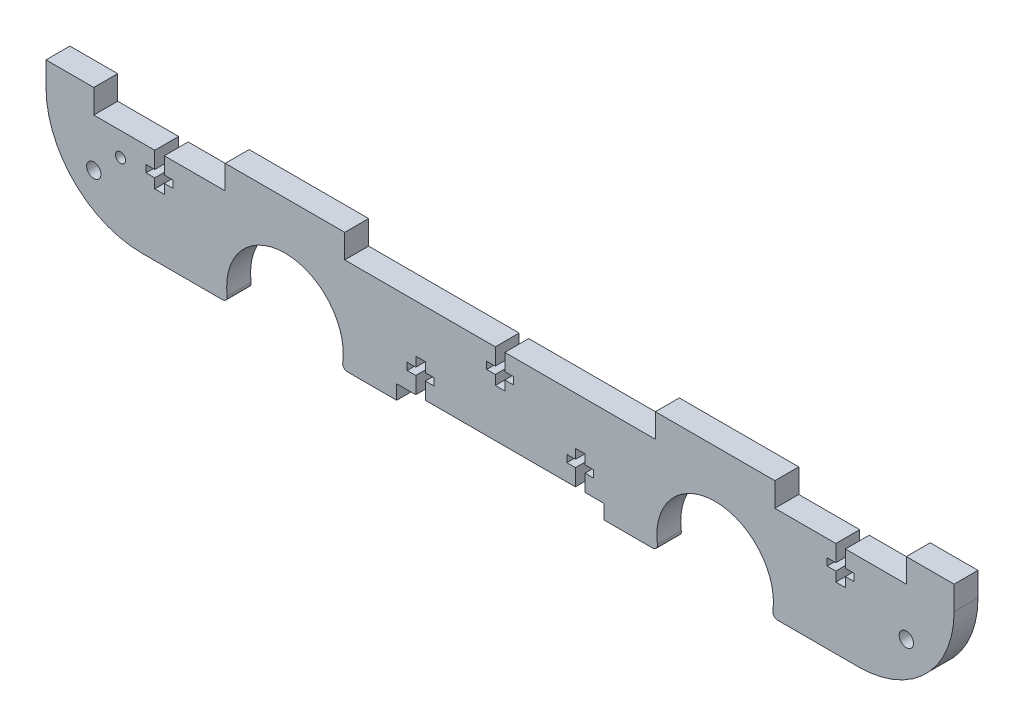
SolidWorks part; units mm, degrees
material "Acrílico (médio-alto impacto)"
ref_plane "Plano frontal" through (0, 0, 0) normal (0, 0, 1) x (1, 0, 0)
ref_plane "Plano superior" through (0, 0, 0) normal (0, 1, 0) x (1, 0, 0)
ref_plane "Plano direito" through (0, 0, 0) normal (1, 0, 0) x (0, 0, -1)
sketch "Esboço1" plane through (0, 0, 0) normal (0, 0, 1) x (1, 0, 0)
  line L1 (20, 0) -> (170, 0)
  line L2 (0, 20) -> (0, 25)
  line L3 (0, 25) -> (190, 25)
  line L4 (190, 20) -> (190, 25)
  arc A0 (0, 20) -> (20, 0) centre (20, 20) ccw
  arc A1 (190, 20) -> (170, 0) centre (170, 20) cw
  point P7 (0, 0)
  point P10 (190, 0)
  dimension "D3" = 20
  dimension "D1" = 190
  dimension "D2" = 25
extrude "Ressalto-extrusão1" add sketch "Esboço1" along normal blind 5
sketch "Esboço2" plane through (0, 0, 0) normal (0, 0, -1) x (-1, 0, 0)
  line L0 (0, 0) -> (-190, 0) construction
  line L1 (0, 25) -> (0, 0) construction
  line L2 (-190, 25) -> (-190, 0) construction
  line L3 (0, 2.8) -> (-190, 2.8) construction
  line L4 (-95, 25) -> (-95, 0) construction
  line L5 (-190, 25) -> (0, 25) construction
  circle A0 centre (-50, 2.8) radius 12.2
  circle A1 centre (-140, 2.8) radius 12.2
  dimension "D1" = 24.4
  dimension "D2" = 50
extrude "Corte-extrusão1" cut sketch "Esboço2" against normal through all
fillet "Filete1" radius 1 4 edges at (38.1257, 0, 2.5) (61.8743, 0, 2.5) (128.1257, 0, 2.5) (151.8743, 0, 2.5)
sketch "Esboço3" plane through (0, 0, 0) normal (0, 0, -1) x (-1, 0, 0)
  line L0 (-152.5, 2.8) -> (-152.5, 25) construction
  line L1 (-190, 25) -> (0, 25) construction
  line L2 (-127.5, 2.8) -> (-127.5, 25) construction
  line L3 (-62.5, 2.8) -> (-62.5, 25) construction
  line L4 (-37.5, 2.8) -> (-37.5, 25) construction
  line L5 (-10, 25) -> (-10, 0) construction
  line L6 (-180, 25) -> (-180, 0) construction
  line L7 (-190, 20) -> (0, 20) construction
  line L8 (-50, 15) -> (-50, 25) construction
  line L9 (-180, 25) -> (-152.5, 25)
  line L10 (-180, 25) -> (-180, 20)
  line L11 (-180, 20) -> (-152.5, 20)
  line L12 (-152.5, 25) -> (-152.5, 20)
  line L13 (-127.5, 25) -> (-62.5, 25)
  line L14 (-127.5, 25) -> (-127.5, 20)
  line L15 (-127.5, 20) -> (-62.5, 20)
  line L16 (-62.5, 25) -> (-62.5, 20)
  line L17 (-37.5, 25) -> (-10, 25)
  line L18 (-37.5, 25) -> (-37.5, 20)
  line L19 (-37.5, 20) -> (-10, 20)
  line L20 (-10, 25) -> (-10, 20)
  line L21 (-190, 25) -> (0, 25) construction
  line L22 (-140, 15) -> (-140, 25) construction
  arc A0 (-127.914, 1.1364) -> (-152.086, 1.1364) centre (-140, 2.8) ccw construction
  arc A1 (-37.914, 1.1364) -> (-62.086, 1.1364) centre (-50, 2.8) ccw construction
  dimension "D1" = 25
  dimension "D2" = 12.5
  dimension "D3" = 25
  dimension "D4" = 12.5
extrude "Corte-extrusão2" cut sketch "Esboço3" against normal through all
sketch "Esboço4" plane through (0, 0, 0) normal (0, 0, -1) x (-1, 0, 0)
  line L0 (-180, 20) -> (-152.5, 20) construction
  line L1 (-127.5, 20) -> (-62.5, 20) construction
  line L2 (-37.5, 20) -> (-10, 20) construction
  line L5 (-37.5, 20) -> (-10, 20) construction
  line L6 (-127.5, 20) -> (-62.5, 20) construction
  line L7 (-180, 20) -> (-152.5, 20) construction
  line B0 (-24.75, 13) -> (-24.75, 15)
  line B1 (-24.75, 13) -> (-22.75, 13)
  line B2 (-24.75, 20) -> (-22.75, 20)
  line B3 (-22.75, 13) -> (-22.75, 15)
  line B4 (-26.55, 15) -> (-24.75, 15)
  line B5 (-26.55, 15) -> (-26.55, 16.5)
  line B6 (-26.55, 16.5) -> (-24.75, 16.5)
  line B7 (-20.95, 15) -> (-20.95, 16.5)
  line B8 (-22.75, 16.5) -> (-22.75, 20)
  line B9 (-22.75, 15) -> (-20.95, 15)
  line B10 (-22.75, 16.5) -> (-20.95, 16.5)
  line B11 (-24.75, 16.5) -> (-24.75, 20)
  line B12 (-96, 13) -> (-96, 15)
  line B13 (-96, 13) -> (-94, 13)
  line B14 (-96, 20) -> (-94, 20)
  line B15 (-94, 13) -> (-94, 15)
  line B16 (-97.8, 15) -> (-96, 15)
  line B17 (-97.8, 15) -> (-97.8, 16.5)
  line B18 (-97.8, 16.5) -> (-96, 16.5)
  line B19 (-92.2, 15) -> (-92.2, 16.5)
  line B20 (-94, 16.5) -> (-94, 20)
  line B21 (-94, 15) -> (-92.2, 15)
  line B22 (-94, 16.5) -> (-92.2, 16.5)
  line B23 (-96, 16.5) -> (-96, 20)
  line B24 (-167.25, 13) -> (-167.25, 15)
  line B25 (-167.25, 13) -> (-165.25, 13)
  line B26 (-167.25, 20) -> (-165.25, 20)
  line B27 (-165.25, 13) -> (-165.25, 15)
  line B28 (-169.05, 15) -> (-167.25, 15)
  line B29 (-169.05, 15) -> (-169.05, 16.5)
  line B30 (-169.05, 16.5) -> (-167.25, 16.5)
  line B31 (-163.45, 15) -> (-163.45, 16.5)
  line B32 (-165.25, 16.5) -> (-165.25, 20)
  line B33 (-165.25, 15) -> (-163.45, 15)
  line B34 (-165.25, 16.5) -> (-163.45, 16.5)
  line B35 (-167.25, 16.5) -> (-167.25, 20)
sketch_block_instance "encaixe_parafuso_acrilico-1"
sketch_block "encaixe_parafuso_acrilico" parameters "D1"=7, "D2"=2, "D3"=5, "D4"=1.5, "D5"=3.5, "D6"=1.5
sketch_block_instance "encaixe_parafuso_acrilico-3"
sketch_block_instance "encaixe_parafuso_acrilico-4"
extrude "Corte-extrusão3" cut sketch "Esboço4" against normal through all
sketch "Esboço5" plane through (0, 0, 5) normal (0, 0, 1) x (1, 0, 0)
  line L0 (95, 0) -> (95, 28.4899) construction
  line L1 (63.0767, 0) -> (126.9233, 0) construction
  line L2 (153.0767, 0) -> (170, 0) construction
  line L3 (190, 20) -> (190, 25) construction
  circle A0 centre (180, 10) radius 1.5
  circle A1 centre (10, 10) radius 1.5
  circle A2 centre (15.5884, 15.0913) radius 1.0364
  dimension "D1" = 3
  dimension "D2" = 10
  dimension "D3" = 10
extrude "Corte-extrusão4" cut sketch "Esboço5" against normal through all
sketch "Esboço6" plane through (0, 0, 5) normal (0, 0, 1) x (1, 0, 0)
  line L0 (153.0767, 0) -> (170, 0) construction
  line L1 (73.3697, 0) -> (116.7699, 0)
  line L2 (73.3697, 0) -> (73.3697, 3)
  line L3 (73.3697, 3) -> (116.7699, 3)
  line L4 (116.7699, 0) -> (116.7699, 3)
  line B0 (112.7699, 10) -> (112.7699, 8)
  line B1 (112.7699, 10) -> (110.7699, 10)
  line B2 (112.7699, 3) -> (110.7699, 3)
  line B3 (110.7699, 10) -> (110.7699, 8)
  line B4 (112.7699, 10) -> (110.7699, 3) construction
  line B5 (112.7699, 3) -> (110.7699, 10) construction
  line B6 (111.7699, 3) -> (111.7699, 11.0263) construction
  line B7 (114.5699, 8) -> (112.7699, 8)
  line B8 (114.5699, 8) -> (114.5699, 6.5)
  line B9 (114.5699, 6.5) -> (112.7699, 6.5)
  line B10 (108.9699, 8) -> (108.9699, 6.5)
  line B11 (114.5699, 8) -> (108.9699, 6.5) construction
  line B12 (114.5699, 6.5) -> (108.9699, 8) construction
  line B13 (110.7699, 6.5) -> (110.7699, 3)
  line B14 (110.7699, 8) -> (108.9699, 8)
  line B15 (110.7699, 6.5) -> (108.9699, 6.5)
  line B16 (112.7699, 6.5) -> (112.7699, 3)
  line B17 (79.3697, 10) -> (79.3697, 8)
  line B18 (79.3697, 10) -> (77.3697, 10)
  line B19 (79.3697, 3) -> (77.3697, 3)
  line B20 (77.3697, 10) -> (77.3697, 8)
  line B21 (79.3697, 10) -> (77.3697, 3) construction
  line B22 (79.3697, 3) -> (77.3697, 10) construction
  line B23 (78.3697, 3) -> (78.3697, 11.0263) construction
  line B24 (81.1697, 8) -> (79.3697, 8)
  line B25 (81.1697, 8) -> (81.1697, 6.5)
  line B26 (81.1697, 6.5) -> (79.3697, 6.5)
  line B27 (75.5697, 8) -> (75.5697, 6.5)
  line B28 (81.1697, 8) -> (75.5697, 6.5) construction
  line B29 (81.1697, 6.5) -> (75.5697, 8) construction
  line B30 (77.3697, 6.5) -> (77.3697, 3)
  line B31 (77.3697, 8) -> (75.5697, 8)
  line B32 (77.3697, 6.5) -> (75.5697, 6.5)
  line B33 (79.3697, 6.5) -> (79.3697, 3)
  dimension "D1" = 5
  dimension "D2" = 5
sketch_block_instance "encaixe_parafuso_acrilico-6"
sketch_block_instance "encaixe_parafuso_acrilico-7"
extrude "Corte-extrusão5" cut sketch "Esboço6" against normal through all contours B33 B26 B25 B24 B17 B18 B20 B31 B27 B32 B30 L3 | L1 L4 L3 L2 | B16 B9 B8 B7 B0 B1 B3 B14 B10 B15 B13 L3
